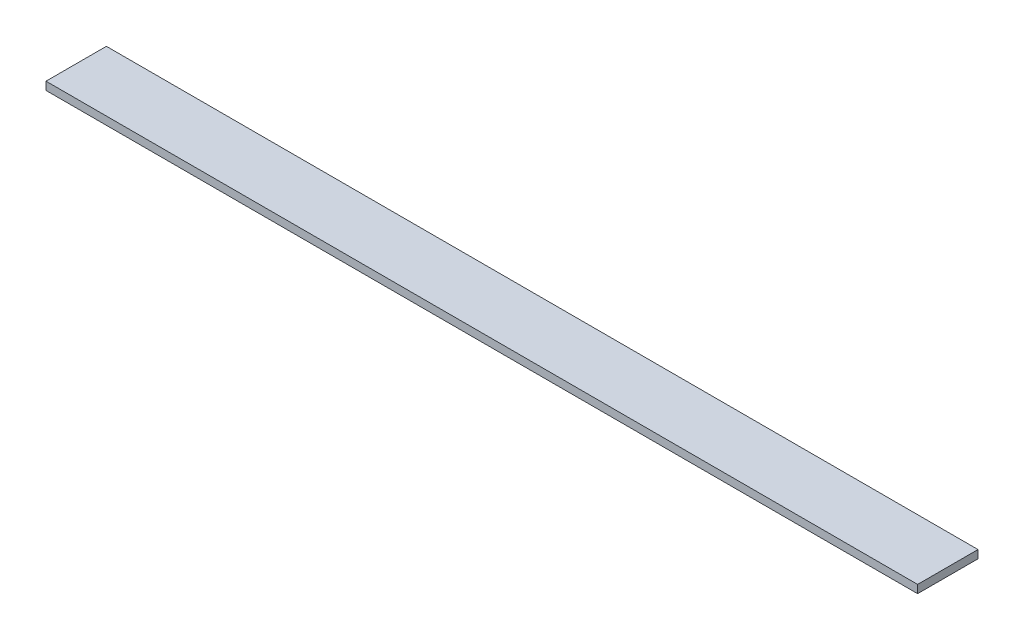
SolidWorks part; units mm, degrees
ref_plane "Спереди" through (0, 0, 0) normal (0, 0, 1) x (1, 0, 0)
ref_plane "Сверху" through (0, 0, 0) normal (0, 1, 0) x (1, 0, 0)
ref_plane "Справа" through (0, 0, 0) normal (1, 0, 0) x (0, 0, -1)
sketch "Эскиз1" plane through (0, 0, 0) normal (1, 0, 0) x (0, 0, -1)
  line L1 (-15, -2) -> (15, -2)
  line L2 (-15, -2) -> (-15, 2)
  line L3 (-15, 2) -> (15, 2)
  line L4 (15, -2) -> (15, 2)
  line L5 (-15, -2) -> (15, 2) construction
  line L6 (-15, 2) -> (15, -2) construction
  point P0 (0, 0)
  dimension "D1" = 4
  dimension "D2" = 30
extrude "Бобышка-Вытянуть1" add sketch "Эскиз1" along normal blind 433
